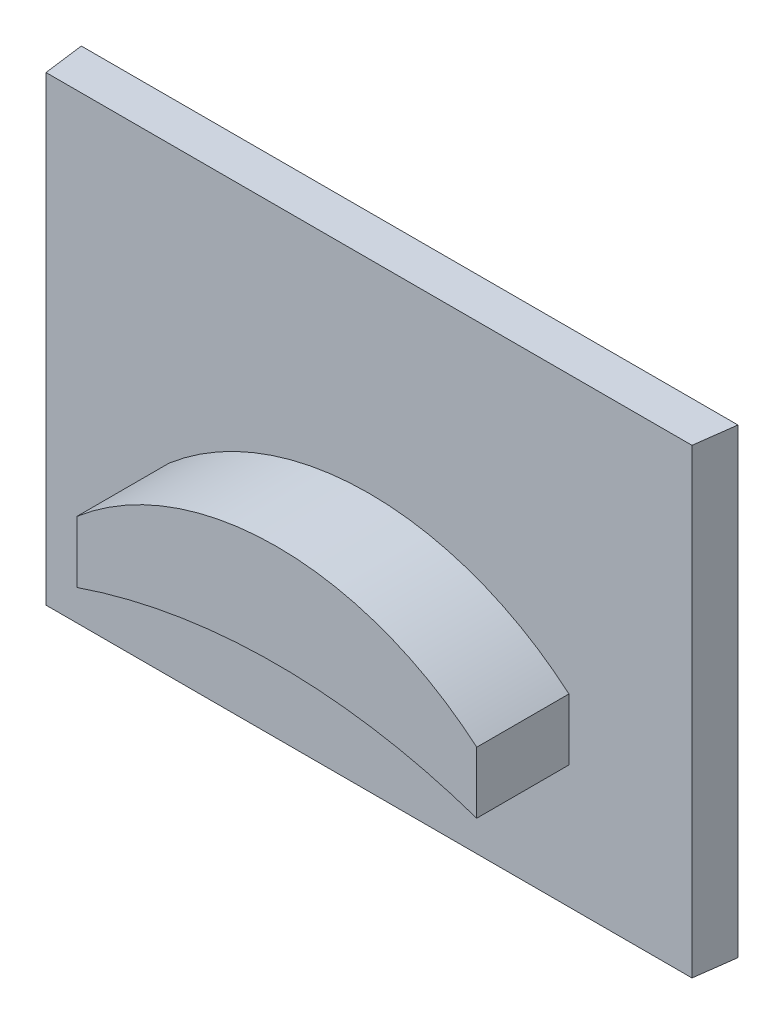
SolidWorks part; units mm, degrees
ref_plane "Plano frontal" through (0, 0, 0) normal (0, 0, 1) x (1, 0, 0)
ref_plane "Plano superior" through (0, 0, 0) normal (0, 1, 0) x (1, 0, 0)
ref_plane "Plano direito" through (0, 0, 0) normal (1, 0, 0) x (0, 0, -1)
sketch "Esboço1" plane through (0, 0, 0) normal (0, 1, 0) x (1, 0, 0)
  line L34 (10.4841, 87.5414) -> (10.6579, 88.8614)
  line L35 (-10.5159, 87.5373) -> (10.4841, 87.5414)
  line L36 (-10.6897, 88.8573) -> (10.6579, 88.8614)
  line L37 (-10.5161, 88.8573) -> (10.4839, 88.8614) construction
  line L38 (-10.6897, 88.8573) -> (-10.5159, 87.5373)
  point P41 (-10.4026, 86.6772)
  point P44 (10.3704, 86.6772)
  dimension "D1" = 97.489
  dimension "D2" = 21
  dimension "D3" = 1.32
extrude "Ressalto-extrusão1" add sketch "Esboço1" along normal blind 15
sketch "Esboço2" plane through (-0.0171, 0, -87.5394) normal (0.0002, 0, 1) x (1, 0, -0.0002)
  line L0 (-6.4987, 6) -> (-6.4987, 4)
  line L1 (6.5013, 4) -> (6.5013, 6)
  line L4 (-10.4987, 0) -> (10.5013, 0)
  line L5 (10.5013, 0) -> (10.5013, 15)
  line L6 (10.5013, 15) -> (-10.4987, 15)
  line L7 (-10.4987, 15) -> (-10.4987, 0)
  line L8 (-10.4987, 0) -> (10.5013, 0)
  line L9 (10.5013, 0) -> (10.5013, 15)
  line L10 (10.5013, 15) -> (-10.4987, 15)
  line L11 (-10.4987, 15) -> (-10.4987, 0)
  line L13 (-6.4987, 15) -> (-6.4987, 0) construction
  line L16 (6.5013, 0) -> (6.5013, 15) construction
  arc A0 (-6.4987, 4) -> (6.5013, 4) centre (0.0013, -14.9143) cw
  arc A1 (-6.4987, 6) -> (6.5013, 6) centre (0.0013, -1.5993) cw
  point P8 (10.1794, 6)
  point P9 (-10.1778, 6)
  point P10 (-10.1778, 4)
  point P11 (10.1794, 4)
  dimension "D5" = 20
  dimension "D9" = 10
  dimension "D6" = 4
  dimension "D7" = 4
  dimension "D4" = 6
  dimension "D11" = 6
  dimension "D1" = 0
  dimension "D2" = 4
  dimension "D3" = 4
extrude "Ressalto-extrusão2" add sketch "Esboço2" along normal blind 3 contours L0 A0 L1 A1
